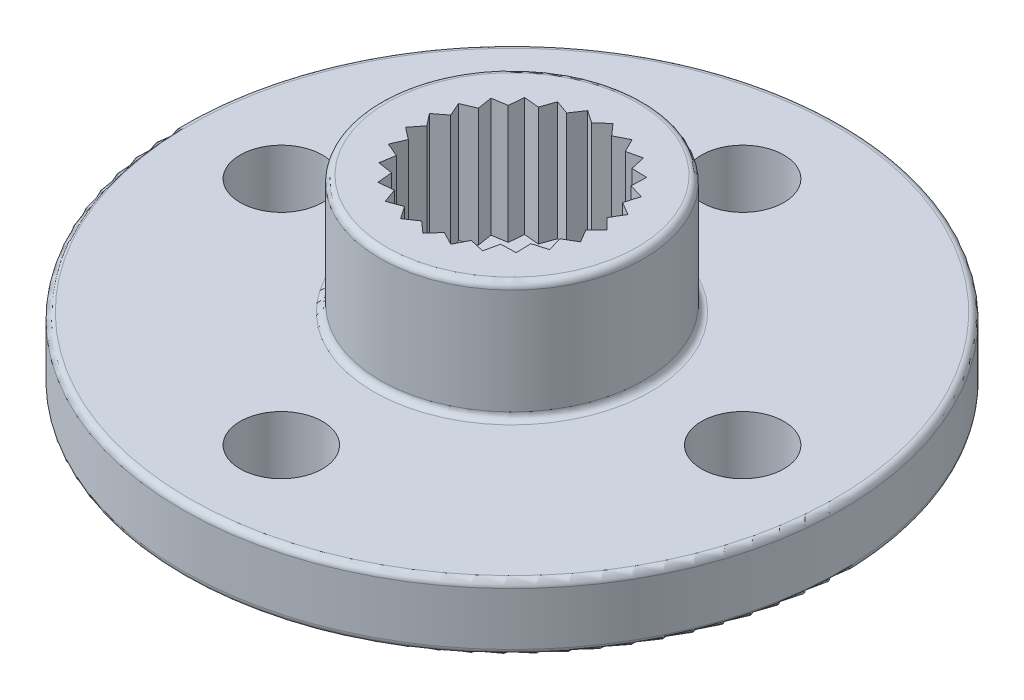
SolidWorks part; units mm, degrees
material "6063-T1"
ref_plane "Plan de face" through (0, 0, 0) normal (0, 0, 1) x (1, 0, 0)
ref_plane "Plan de dessus" through (0, 0, 0) normal (0, 1, 0) x (1, 0, 0)
ref_plane "Plan de droite" through (0, 0, 0) normal (1, 0, 0) x (0, 0, -1)
ref_plane "Plan1" through (0, 0, 0) normal (0, 0, -1) x (-1, 0, 0)
sketch "Sketch2" plane through (0, 0, 0) normal (0, 1, 0) x (1, 0, 0)
  circle A0 centre (0, 0) radius 10
  dimension "D1" = 20
extrude "Boss-Extrude1" add sketch "Sketch2" along normal blind 2
sketch "Sketch3" plane through (0, 2, 0) normal (0, 1, 0) x (1, 0, 0)
  circle A0 centre (0, 0) radius 4
  dimension "D1" = 8
extrude "Boss-Extrude2" add sketch "Sketch3" along normal blind 3.6
hole_wizard "M3x0.5 Tapped Hole1" positions "Sketch5" profile "Sketch4" tap size "M3x0.5" standard "ANSI Metric" end condition through all
sketch "Sketch5" plane through (0, 2, 0) normal (0, 1, 0) x (1, 0, 0)
  line L0 (0, 7) -> (0, -7) construction
  line L2 (7, 0) -> (-7, 0) construction
  point P0 (0, 7)
  point P2 (-7, 0)
  point P4 (0, -7)
  point P6 (7, 0)
  dimension "D1" = 14
cosmetic thread "Hole Thread5" parameters "D2"=3
cosmetic thread "Hole Thread6" parameters "D2"=3
cosmetic thread "Hole Thread7" parameters "D2"=3
cosmetic thread "Hole Thread8" parameters "D2"=3
sketch "Sketch4" plane through (0, 2, -7) normal (1, 0, 0) x (0, 0, 1)
  line L0 (0, 0) -> (0, 2)
  line L1 (0, 2) -> (1.25, 2)
  line L2 (1.25, 2) -> (1.25, 0)
  line L5 (1.25, 0) -> (0, 0)
  line L11 (0, -6.35) -> (0, 107.95) construction
  dimension "Thru Tap Drill Dia." = 2.5
  dimension "Thru Tap Drill Depth" = 2
sketch "Sketch6" plane through (0, 5.6, 0) normal (0, 1, 0) x (1, 0, 0)
  circle A0 centre (0, 0) radius 2.585
  dimension "D1" = 5.17
extrude "Cut-Extrude1" cut sketch "Sketch6" against normal blind 3.6
sketch "Sketch7" plane through (0, 2, 0) normal (0, 1, 0) x (1, 0, 0)
  circle A0 centre (0, 0) radius 1.5
  dimension "D1" = 3
extrude "Cut-Extrude2" cut sketch "Sketch7" against normal through all
fillet "Fillet1" radius 0.2 4 edges at (0, 5.6, 4) (0, 2, 4) (0, 2, 10) (0, 0, 10)
sketch "Sketch8" plane through (0, 5.6, 0) normal (0, 1, 0) x (1, 0, 0)
  line L0 (0, 0) -> (2.89, 0) construction
  line L1 (0, 0) -> (2.5646, 0.324) construction
  line L2 (0, 0) -> (2.5646, -0.324) construction
  line L3 (2.5646, 0.324) -> (2.89, 0)
  line L4 (2.89, 0) -> (2.5646, -0.324)
  arc A1 (2.5646, -0.324) -> (2.5646, 0.324) centre (0, 0) ccw
  circle A2 centre (0, 0) radius 2.89 construction
  circle A3 centre (0, 0) radius 2.585 construction
  dimension "D3" = 5.78
  dimension "D1" = 14.4
extrude "Cut-Extrude6" cut sketch "Sketch8" against normal up to surface (3.6 mm away) up to face at (0, 2, 1.5)
pattern_circular "CirPattern1" count 25 over 360 about axis through (0, 0, 0) along (0, 1, 0) of "Cut-Extrude6"
chamfer "Chamfer1" distance 0.5 angle 45 1 edges at (0, 0, 1.5)
